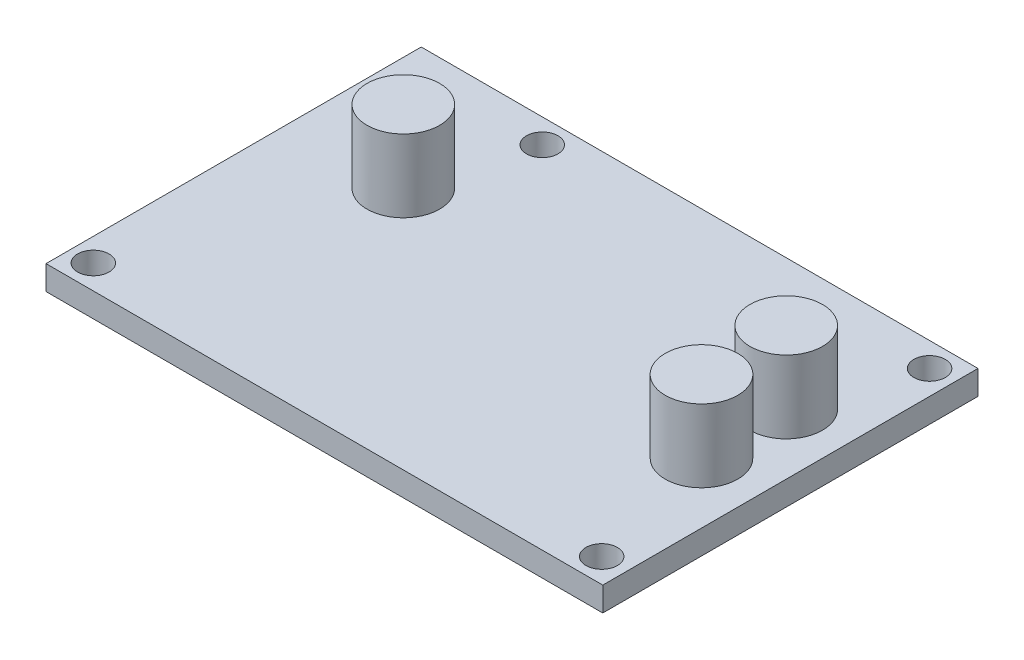
SolidWorks part; units mm, degrees
material "6061-T6 (SS)"
ref_plane "Front Plane" through (0, 0, 0) normal (0, 0, 1) x (1, 0, 0)
ref_plane "Top Plane" through (0, 0, 0) normal (0, 1, 0) x (1, 0, 0)
ref_plane "Right Plane" through (0, 0, 0) normal (1, 0, 0) x (0, 0, -1)
sketch "Sketch1" plane through (0, 0, 0) normal (0, 1, 0) x (1, 0, 0)
  line L1 (0, 0) -> (58.42, 0)
  line L2 (0, 0) -> (0, 39.37)
  line L3 (0, 39.37) -> (58.42, 39.37)
  line L4 (58.42, 0) -> (58.42, 39.37)
  dimension "D1" = 58.42
  dimension "D2" = 39.37
extrude "Boss-Extrude1" add sketch "Sketch1" along normal blind 2.54
sketch "Sketch2" plane through (0, 2.54, 0) normal (0, 1, 0) x (1, 0, 0)
  line L0 (0, 0) -> (58.42, 0) construction
  line L2 (58.42, 0) -> (58.42, 39.37) construction
  circle A0 centre (2.4247, 2.54) radius 1.651
  circle A1 centre (55.7647, 2.54) radius 1.651
  circle A2 centre (15.24, 36.83) radius 1.651
  circle A3 centre (55.88, 36.8298) radius 1.651
  dimension "D1" = 3.302
  dimension "D2" = 3.302
  dimension "D3" = 3.302
  dimension "D4" = 3.302
  dimension "D5" = 34.29
  dimension "D6" = 2.54
  dimension "D7" = 2.54
  dimension "D8" = 34.29
  dimension "D9" = 40.64
  dimension "D10" = 53.34
  dimension "D12" = 2.54
  dimension "D13" = 2.6553
extrude "Cut-Extrude1" cut sketch "Sketch2" against normal up to next
sketch "Sketch3" plane through (0, 2.54, 0) normal (0, 1, 0) x (1, 0, 0)
  line L0 (58.42, 0) -> (58.42, 39.37) construction
  circle A0 centre (52.07, 25.5979) radius 3.81
  circle A1 centre (52.07, 16.7079) radius 3.81
  circle A2 centre (11.895, 25.5979) radius 3.81
  dimension "D1" = 7.62
  dimension "D2" = 7.62
  dimension "D3" = 8.89
  dimension "D4" = 6.35
  dimension "D5" = 6.35
  dimension "D6" = 7.62
extrude "Boss-Extrude2" add sketch "Sketch3" along normal blind 7.62
